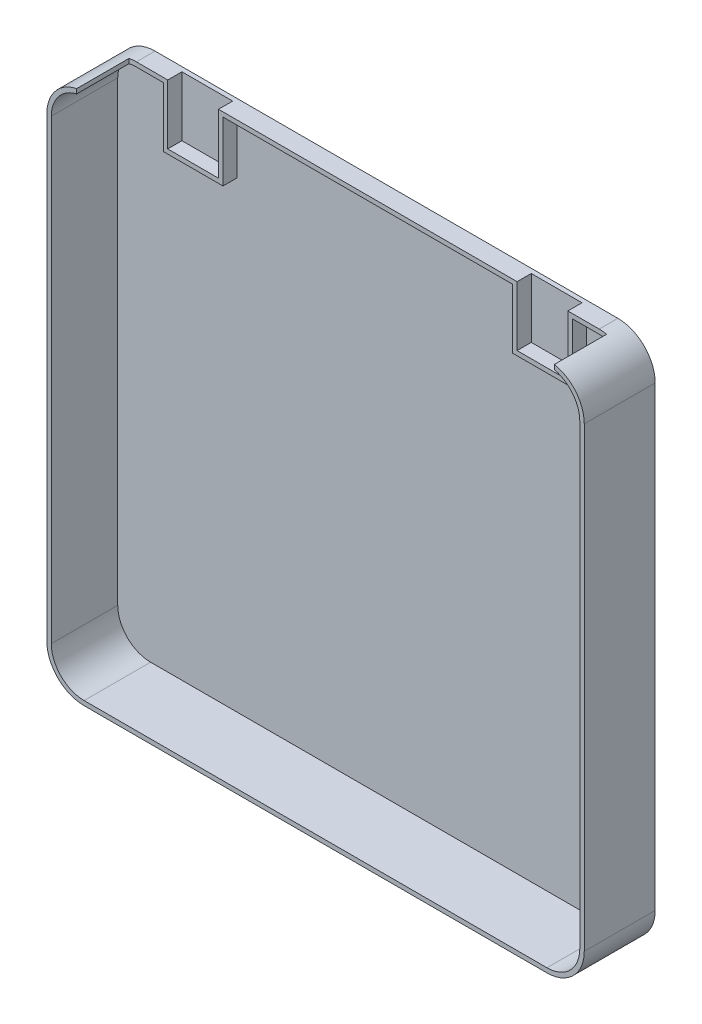
SolidWorks part; units mm, degrees
ref_plane "Plan de face" through (0, 0, 0) normal (0, 0, 1) x (1, 0, 0)
ref_plane "Plan de dessus" through (0, 0, 0) normal (0, 1, 0) x (1, 0, 0)
ref_plane "Plan de droite" through (0, 0, 0) normal (1, 0, 0) x (0, 0, -1)
sketch "Esquisse1" plane through (0, 0, 0) normal (0, 0, 1) x (1, 0, 0)
  line L1 (0, 0) -> (360, 0)
  line L2 (0, 0) -> (0, 356)
  line L3 (0, 356) -> (360, 356)
  line L4 (360, 0) -> (360, 356)
  dimension "D1" = 360
  dimension "D2" = 356
extrude "Boss.-Extru.1" add sketch "Esquisse1" along normal blind 47.5
fillet "Congé1" radius 25 4 edges at (0, 0, 23.75) (360, 0, 23.75) (360, 356, 23.75) (0, 356, 23.75)
sketch "Esquisse2" plane through (0, 0, 47.5) normal (0, 0, 1) x (1, 0, 0)
  line L8 (3, 331) -> (3, 25)
  line L9 (25, 3) -> (335, 3)
  line L10 (357, 25) -> (357, 331)
  line L11 (335, 353) -> (25, 353)
  line L12 (3, 331) -> (3, 25)
  line L13 (25, 3) -> (335, 3)
  line L14 (357, 25) -> (357, 331)
  line L15 (335, 353) -> (25, 353)
  arc A8 (3, 25) -> (25, 3) centre (25, 25) ccw
  arc A9 (335, 3) -> (357, 25) centre (335, 25) ccw
  arc A10 (357, 331) -> (335, 353) centre (335, 331) ccw
  arc A11 (25, 353) -> (3, 331) centre (25, 331) ccw
  arc A12 (3, 25) -> (25, 3) centre (25, 25) ccw
  arc A13 (335, 3) -> (357, 25) centre (335, 25) ccw
  arc A14 (357, 331) -> (335, 353) centre (335, 331) ccw
  arc A15 (25, 353) -> (3, 331) centre (25, 331) ccw
  dimension "D1" = 3
extrude "Enlèv. mat.-Extru.1" cut sketch "Esquisse2" against normal blind 44.5 contours L12 A12 L13 A13 L14 A14 L15 A15
sketch "Esquisse3" plane through (0, 356, 0) normal (0, 1, 0) x (1, 0, 0)
  line L0 (335, -47.5) -> (25, -47.5) construction
  line L1 (20, -47.5) -> (340, -47.5)
  line L2 (20, -47.5) -> (20, -12.5)
  line L3 (20, -12.5) -> (340, -12.5)
  line L4 (340, -47.5) -> (340, -12.5)
  line L5 (0, -47.5) -> (0, 0) construction
  dimension "D1" = 35
  dimension "D2" = 320
  dimension "D3" = 20
extrude "Enlèv. mat.-Extru.2" cut sketch "Esquisse3" against normal blind 10 contours L2 L1 L4 L3
sketch "Esquisse4" plane through (0, 3, 0) normal (0, 1, 0) x (1, 0, 0)
  line L0 (180, 0) -> (180, -47.5) construction
  line L1 (335, 0) -> (25, 0) construction
  line L2 (25, -47.5) -> (335, -47.5) construction
sketch "Esquisse5" plane through (0, 0, 3) normal (0, 0, 1) x (1, 0, 0)
  line L0 (180, 99.9998) -> (180, 353) construction
  line L1 (25, 353) -> (335, 353) construction
  line L2 (335, 353) -> (25, 353) construction
  line L3 (43, 353) -> (83, 353)
  line L4 (43, 353) -> (43, 313)
  line L5 (43, 313) -> (83, 313)
  line L6 (83, 353) -> (83, 313)
  line L7 (3, 331) -> (3, 25) construction
  line L8 (317, 313) -> (277, 313)
  line L9 (277, 353) -> (277, 313)
  line L10 (317, 353) -> (277, 353)
  line L11 (317, 353) -> (317, 313)
  point P6 (180, 353)
  line M17 (335, 353) -> (25, 353)
  dimension "D1" = 40
  dimension "D2" = 40
  dimension "D3" = 40
extrude "Extru.-Mince1" add sketch "Esquisse5" along normal blind 9.5 thin contours L6 L4 L5 M17 | L8 L9 L10 L11
sketch "Esquisse9" plane through (0, 0, 12.5) normal (0, 0, 1) x (1, 0, 0)
  line L0 (314, 350) -> (314, 356) construction
  line L1 (25, 356) -> (335, 356) construction
  line L2 (280, 350) -> (280, 356) construction
sketch "Esquisse10" plane through (0, 356, 0) normal (0, 1, 0) x (1, 0, 0)
  line L0 (25, -12.5) -> (335, -12.5) construction
  line L1 (280, -12.5) -> (314, -12.5)
  line L2 (280, -12.5) -> (280, -3)
  line L3 (280, -3) -> (314, -3)
  line L4 (314, -12.5) -> (314, -3)
  dimension "D1" = 9.5
  dimension "D2" = 34
  dimension "D3" = 0
extrude "Enlèv. mat.-Extru.4" cut sketch "Esquisse10" against normal blind 10 contours L2 L1 L4 L3
sketch "Esquisse12" plane through (0, 0, 12.5) normal (0, 0, 1) x (1, 0, 0)
  line L0 (46, 350) -> (46, 356) construction
  line L1 (25, 356) -> (280, 356) construction
  line L2 (80, 350) -> (80, 356) construction
sketch "Esquisse13" plane through (0, 356, 0) normal (0, 1, 0) x (1, 0, 0)
  line L0 (25, -12.5) -> (280, -12.5) construction
  line L1 (46, -12.5) -> (80, -12.5)
  line L2 (46, -12.5) -> (46, -3)
  line L3 (46, -3) -> (80, -3)
  line L4 (80, -12.5) -> (80, -3)
  dimension "D1" = 34
  dimension "D2" = 9.5
  dimension "D3" = 0
  dimension "D4" = 0
extrude "Enlèv. mat.-Extru.5" cut sketch "Esquisse13" against normal blind 10
